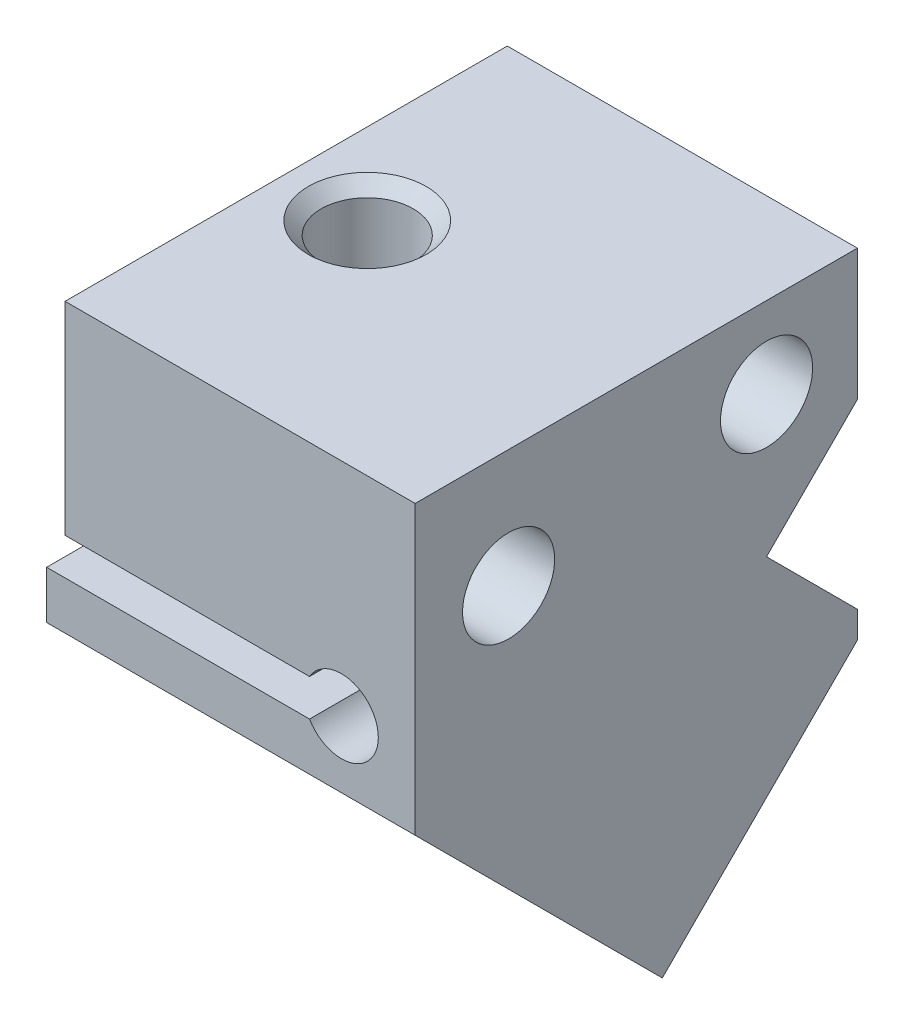
SolidWorks part; units mm, degrees
material "2024-T4"
ref_plane "Front" through (0, 0, 0) normal (0, 0, 1) x (1, 0, 0)
ref_plane "Top" through (0, 0, 0) normal (0, 1, 0) x (1, 0, 0)
ref_plane "Right" through (0, 0, 0) normal (1, 0, 0) x (0, 0, -1)
sketch "Эскиз1" plane through (0, 0, 0) normal (1, 0, 0) x (0, 0, -1)
  line L0 (0, 0) -> (12, 0)
  line L1 (12, 0) -> (12, -9.2132)
  line L3 (6.7071, -14.5061) -> (0, -7.799)
  line L4 (0, -7.799) -> (0, 0)
  line L5 (12, -9.2132) -> (6.7071, -14.5061)
  dimension "D1" = 12
  dimension "D2" = 14
  dimension "D4" = 15
  dimension "D6" = 45
extrude "Бобышка-Вытянуть1" add sketch "Эскиз1" along normal blind 10
sketch "Эскиз2" plane through (0, -10.6066, -10.6066) normal (0, -0.7071, -0.7071) x (-1, 0, 0)
  line L1 (-9, 7.6065) -> (-1, 7.6065)
  line L2 (-9, 7.6065) -> (-9, -8.1315)
  line L3 (-9, -8.1315) -> (-1, -8.1315)
  line L4 (-1, 7.6065) -> (-1, -8.1315)
  line L7 (0, -5.5147) -> (0, 1.9706) construction
  dimension "D1" = 1
  dimension "D2" = 8
extrude "Вырез-Вытянуть1" cut sketch "Эскиз2" against normal blind 2
sketch "Эскиз3" plane through (0, 0, 0) normal (0, 0, 1) x (1, 0, 0)
  line L0 (0.5, 0) -> (0.5, -5.5)
  line L1 (10, 0) -> (0, 0) construction
  line L2 (0.5, -5.5) -> (7.134, -5.5)
  line L3 (10, 0) -> (10, -7.799) construction
  line L4 (7.134, -6.5) -> (0, -6.5)
  line L5 (0, 0) -> (0, -7.799) construction
  arc A0 (7.134, -5.5) -> (7.134, -6.5) centre (8, -6) cw
  line M1 (0, 0) -> (0, -7.799)
  line M4 (10, 0) -> (0, 0)
  dimension "D4" = 1
  dimension "D6" = 6
  dimension "D1" = 6.5
  dimension "D2" = 1
  dimension "D3" = 0.5
  dimension "D5" = 2
extrude "Вырез-Вытянуть2" cut sketch "Эскиз3" against normal through all contours L4 A0 L2 L0 M4 M1
hole_wizard "Отверстие обработанное метчиком M31" positions "Эскиз5" profile "Эскиз4" tap size "M3" standard "DIN" end condition through all
sketch "Эскиз5" plane through (0, 0, 0) normal (-1, 0, 0) x (0, 0, 1)
  line L0 (-5.2929, -13.0919) -> (-12, -6.3848) construction
  line L1 (0, -7.799) -> (-6.7071, -14.5061) construction
  point P1 (-9.5355, -2.2024)
  point P4 (-2.5355, -3.2024)
  dimension "D1" = 7
  dimension "D2" = 1
  dimension "D3" = 4.7
  dimension "D4" = 10.7
sketch "Эскиз4" plane through (0, -2.2024, -9.5355) normal (0, 1, 0) x (0, 0, 1)
  line L0 (0, 0) -> (0, 10)
  line L1 (0, 10) -> (1.25, 10)
  line L2 (1.25, 10) -> (1.25, 0.4)
  line L3 (1.25, 0.4) -> (1.65, 0)
  line L5 (1.65, 0) -> (0, 0)
  line L6 (-1.25, 0.4) -> (-1.65, 0) construction
  line L11 (0, -6.35) -> (0, 107.95) construction
  dimension "Диаметр проходного сверла" = 2.5
  dimension "Глубина проходного сверла" = 10
  dimension "Диаметр передней зенковки" = 3.3
  dimension "Угол передней зенковки" = 90
cosmetic thread "Отверстие резьбы6" parameters "D1"=6, "D2"=3
cosmetic thread "Отверстие резьбы7" parameters "D1"=6, "D2"=3
hole_wizard "Отверстие обработанное метчиком M32" positions "Эскиз7" profile "Эскиз6" tap size "M3" standard "DIN" end condition up to next
sketch "Эскиз7" plane through (0, 0, 0) normal (0, 1, 0) x (-1, 0, 0)
  line L0 (-0.5, -12) -> (-0.5, 0) construction
  line L2 (-10, 0) -> (-0.5, 0) construction
  point P0 (-2.7, -6)
  dimension "D1" = 2.2
  dimension "D2" = 6
cosmetic thread "Отверстие резьбы3" parameters "D2"=3
sketch "Эскиз6" plane through (2.7, 0, -6) normal (1, 0, 0) x (0, 0, 1)
  line L0 (0, 0) -> (0, 5.5)
  line L1 (0, 5.5) -> (1.25, 5.5)
  line L2 (1.25, 5.5) -> (1.25, 0.35)
  line L3 (1.25, 0.35) -> (1.6, 0)
  line L5 (1.6, 0) -> (0, 0)
  line L6 (-1.25, 0.35) -> (-1.6, 0) construction
  line L11 (0, -6.35) -> (0, 107.95) construction
  dimension "Диаметр проходного сверла" = 2.5
  dimension "Глубина проходного сверла" = 5.5
  dimension "Диаметр передней зенковки" = 3.2
  dimension "Угол передней зенковки" = 90
sketch "Эскиз9" plane through (0, -3.8995, 3.8995) normal (0, -0.7071, 0.7071) x (1, 0, 0)
  line L1 (11.6012, -16.398) -> (-3.7671, -16.398)
  line L2 (11.6012, -16.398) -> (11.6012, -11)
  line L3 (11.6012, -11) -> (-3.7671, -11)
  line L4 (-3.7671, -16.398) -> (-3.7671, -11)
  line L5 (1, -15) -> (0, -15) construction
  dimension "D1" = 4
extrude "Вырез-Вытянуть3" cut sketch "Эскиз9" against normal blind 4 from offset 8
